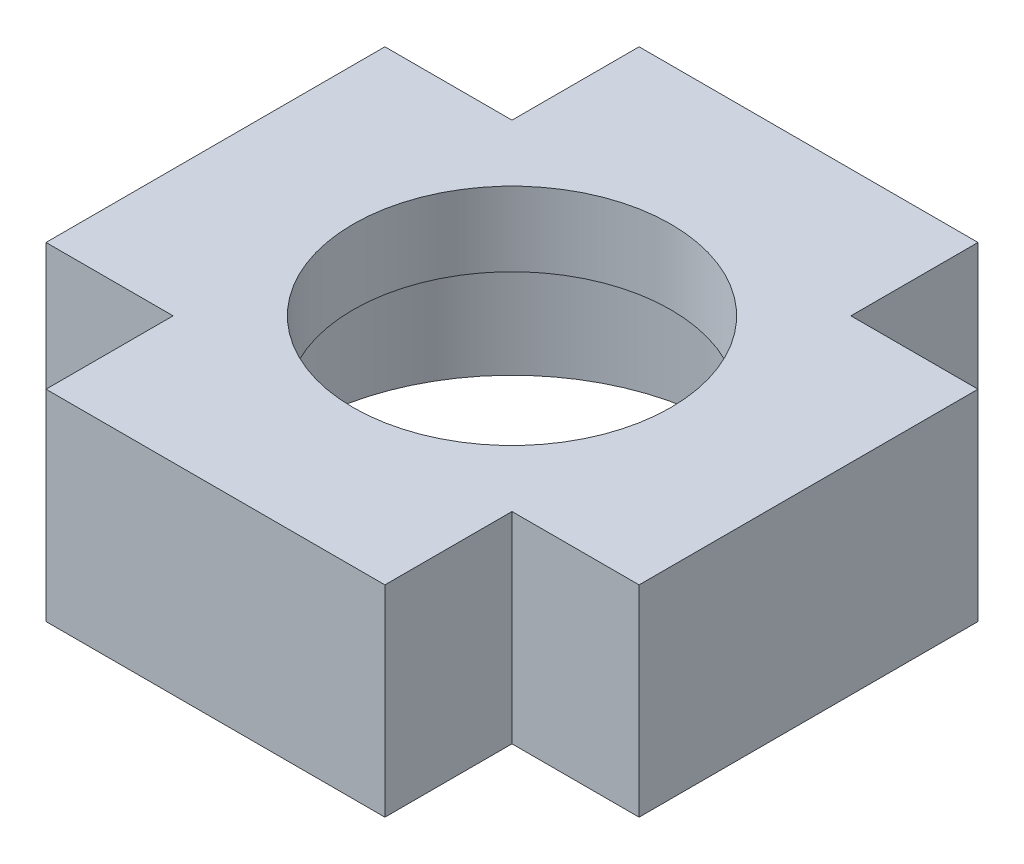
SolidWorks part; units mm, degrees
ref_plane "前视基准面" through (0, 0, 0) normal (0, 0, 1) x (1, 0, 0)
ref_plane "上视基准面" through (0, 0, 0) normal (0, 1, 0) x (1, 0, 0)
ref_plane "右视基准面" through (0, 0, 0) normal (1, 0, 0) x (0, 0, -1)
other "Configuration Table"
sketch "草图1" plane through (0, 0, 0) normal (0, 1, 0) x (1, 0, 0)
  line L0 (-8, 14) -> (8, 14)
  line L1 (8, 14) -> (8, 8)
  line L2 (8, 8) -> (14, 8)
  line L3 (14, 8) -> (14, -8)
  line L4 (14, -8) -> (8, -8)
  line L5 (8, -8) -> (8, -14)
  line L6 (8, -14) -> (-8, -14)
  line L7 (-8, -14) -> (-8, -8)
  line L8 (-8, -8) -> (-14, -8)
  line L9 (-14, -8) -> (-14, 8)
  line L10 (-14, 8) -> (-8, 8)
  line L11 (-8, 8) -> (-8, 14)
  line L12 (0, 0) -> (0, 20.7439) construction
  line L13 (-23.5044, 0) -> (4.4956, 0) construction
  circle A1 centre (0, 0) radius 7.5
  point P16 (0, 14)
  point P18 (14, 0)
  dimension "D7" = 15
  dimension "D1" = 28
  dimension "D2" = 6
  dimension "D3" = 6
  dimension "D4" = 28
  dimension "D5" = 6
  dimension "D6" = 6
extrude "凸台-拉伸1" add sketch "草图1" along normal blind 9.5
sketch "草图2" plane through (0, 0, 0) normal (0, -1, 0) x (1, 0, 0)
  circle A0 centre (0, 0) radius 10
  dimension "D1" = 20
extrude "切除-拉伸1" cut sketch "草图2" against normal blind 6
